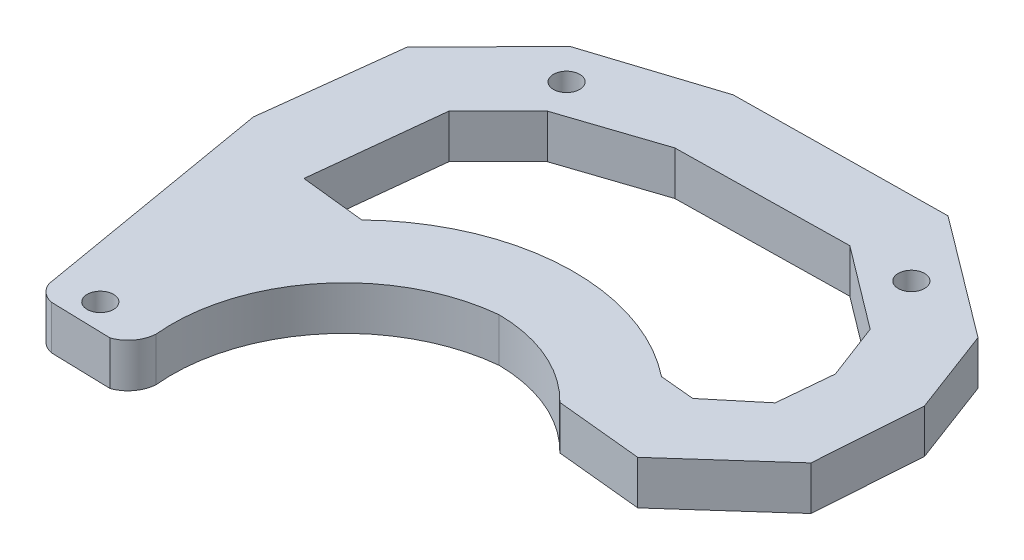
SolidWorks part; units mm, degrees
ref_plane "Front Plane" through (0, 0, 0) normal (0, 0, 1) x (1, 0, 0)
ref_plane "Top Plane" through (0, 0, 0) normal (0, 1, 0) x (1, 0, 0)
ref_plane "Right Plane" through (0, 0, 0) normal (1, 0, 0) x (0, 0, -1)
sketch "Sketch1" plane through (0, 0, 0) normal (0, 1, 0) x (1, 0, 0)
  line L0 (-107.4272, 18.982) -> (-55.563, 18.982) construction
  line L34 (10.4868, 505.3856) -> (650.4868, 505.3856) construction
  line L56 (1.0369, 38.7437) -> (-0.5785, 23.8114)
  line L57 (1.5697, 52.0403) -> (15.6513, 56.5598)
  line L58 (-7.6683, 42.6844) -> (1.5697, 52.0403)
  line L59 (39.3956, 24.6288) -> (43.3401, 24.2585)
  line L60 (48.4762, 28.5252) -> (43.3401, 24.2585)
  line L61 (6.6424, 44.3491) -> (17.556, 47.9852)
  line L62 (36.1485, 16.2828) -> (46.0126, 15.3019)
  line L63 (53.5994, 46.5351) -> (57.2911, 36.7386)
  line L64 (-9.5446, 27.0087) -> (-7.6683, 42.6844)
  line L65 (46.0126, 15.3019) -> (56.4485, 24.6288)
  line L66 (39.8562, 56.8586) -> (53.5994, 46.5351)
  line L67 (-9.5446, 27.0087) -> (-4.7334, -1.0891)
  line L68 (49.0569, 34.8048) -> (48.4762, 28.5252)
  line L69 (-2.7714, -2.8203) -> (4.1071, -3.0049)
  line L70 (15.6513, 56.5598) -> (39.8562, 56.8586)
  line L71 (56.4485, 24.6288) -> (57.2911, 36.7386)
  line L72 (1.0369, 38.7437) -> (6.6424, 44.3491)
  line L73 (46.6194, 41.2127) -> (49.0569, 34.8048)
  line L74 (17.556, 47.9852) -> (37.1977, 48.3126)
  line L75 (37.1977, 48.3126) -> (46.6194, 41.2127)
  line L76 (-0.5785, 23.8114) -> (6.8244, 23.0105)
  arc A14 (6.8244, 23.0105) -> (39.3956, 24.6288) centre (24.0304, 5.2954) cw
  arc A15 (6.3643, 0) -> (24.0304, 21.481) centre (25.9378, 1.9075) cw
  arc A16 (4.1071, -3.0049) -> (6.3643, 0) centre (2.9781, 0.1934) ccw
  arc A17 (-4.7334, -1.0891) -> (-2.7714, -2.8203) centre (-2.2064, -0.2026) ccw
  arc A18 (24.0304, 21.481) -> (36.1485, 16.2828) centre (23.8619, 4.3641) cw
  dimension "D2" = 24.2049
extrude "Boss-Extrude2" add sketch "Sketch1" along normal blind 5
sketch "Sketch2" plane through (0, 5, 0) normal (0, 1, 0) x (1, 0, 0)
  circle A0 centre (44.1945, 48.3351) radius 1.5
  circle A1 centre (0, 0) radius 1.5
  circle A2 centre (4.8594, 48.3351) radius 1.5
  dimension "D1" = 3
  dimension "D2" = 3
  dimension "D4" = 3
extrude "Cut-Extrude1" cut sketch "Sketch2" against normal blind 15
